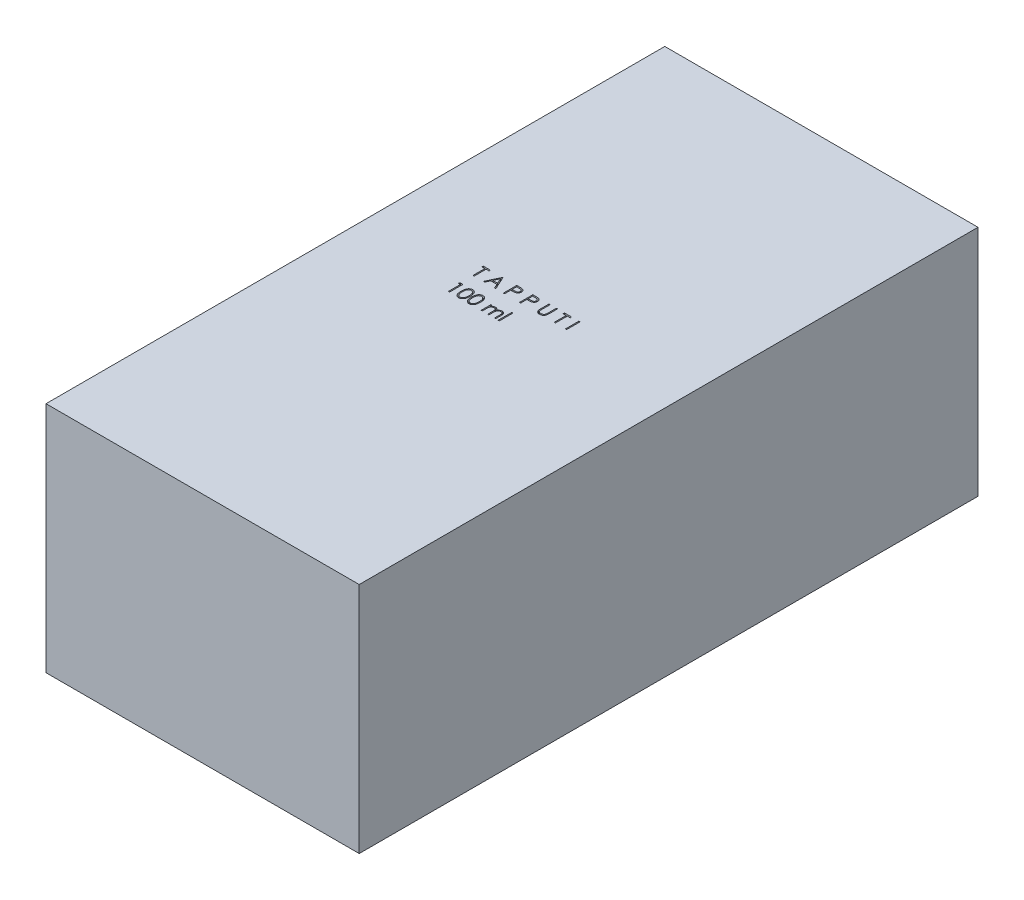
SolidWorks part; units mm, degrees
ref_plane "Front Plane" through (0, 0, 0) normal (0, 0, 1) x (1, 0, 0)
ref_plane "Top Plane" through (0, 0, 0) normal (0, 1, 0) x (1, 0, 0)
ref_plane "Right Plane" through (0, 0, 0) normal (1, 0, 0) x (0, 0, -1)
sketch "Sketch1" plane through (0, 0, 0) normal (0, 1, 0) x (1, 0, 0)
  line L1 (-41, 81) -> (41, 81)
  line L2 (-41, 81) -> (-41, -81)
  line L3 (-41, -81) -> (41, -81)
  line L4 (41, 81) -> (41, -81)
  line L5 (-41, 81) -> (41, -81) construction
  line L6 (-41, -81) -> (41, 81) construction
  point P0 (0, 0)
  dimension "D1" = 82
  dimension "D2" = 162
extrude "Boss-Extrude1" add sketch "Sketch1" against normal blind 61
sketch "Sketch3" plane through (0, 0, 0) normal (0, 1, 0) x (1, 0, 0)
  text T0 "T A P P U T I\r\n100 ml"
extrude "Cut-Extrude1" cut sketch "Sketch3" against normal blind 10
